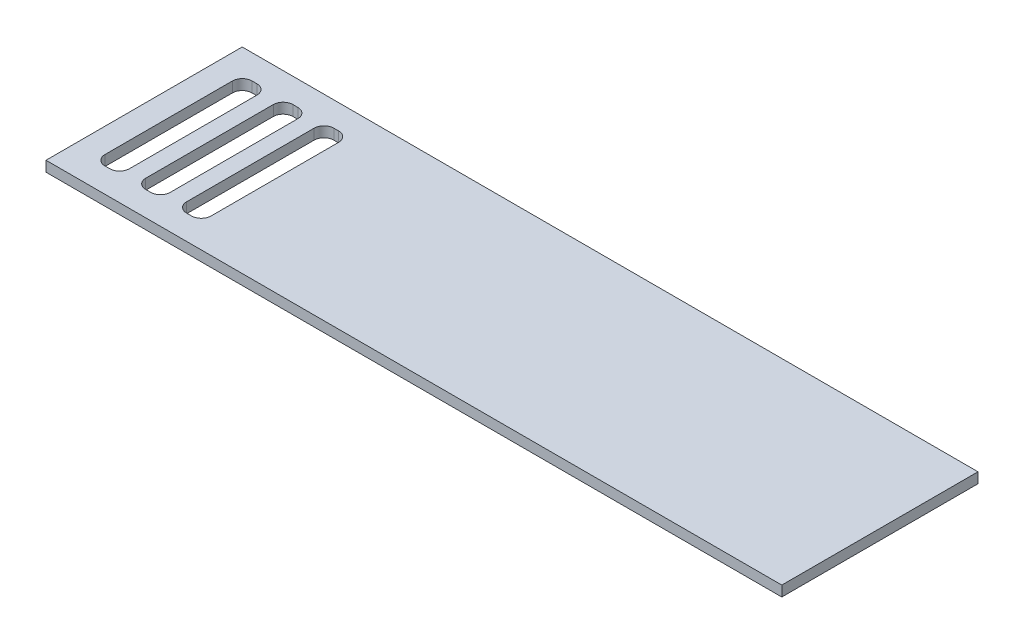
SolidWorks part; units mm, degrees
ref_plane "Front Plane" through (0, 0, 0) normal (0, 0, 1) x (1, 0, 0)
ref_plane "Top Plane" through (0, 0, 0) normal (0, 1, 0) x (1, 0, 0)
ref_plane "Right Plane" through (0, 0, 0) normal (1, 0, 0) x (0, 0, -1)
sketch "Sketch1" plane through (0, 0, 0) normal (0, 1, 0) x (1, 0, 0)
  line L1 (0, 0) -> (450, 0)
  line L2 (0, 0) -> (0, 120)
  line L3 (0, 120) -> (450, 120)
  line L4 (450, 0) -> (450, 120)
extrude "Boss-Extrude1" add sketch "Sketch1" along normal blind 6.35
sketch "Sketch2" plane through (0, 6.35, 0) normal (0, 1, 0) x (1, 0, 0)
  line L5 (15, 15) -> (15, 105)
  line L6 (15, 105) -> (30, 105)
  line L7 (30, 105) -> (30, 15)
  line L8 (30, 15) -> (15, 15)
  line L10 (40, 105) -> (55, 105)
  line L11 (55, 105) -> (55, 15)
  line L12 (55, 15) -> (40, 15)
  line L13 (40, 15) -> (40, 105)
  line L15 (65, 105) -> (65, 15)
  line L16 (65, 15) -> (80, 15)
  line L17 (80, 15) -> (80, 105)
  line L18 (80, 105) -> (65, 105)
extrude "Cut-Extrude1" cut sketch "Sketch2" against normal through all both and the other way through all
fillet "Fillet1" radius 6 12 edges at (80, 3.175, -15) (55, 3.175, -15) (30, 3.175, -15) (65, 3.175, -15) (40, 3.175, -15) (15, 3.175, -15) (15, 3.175, -105) (40, 3.175, -105) (65, 3.175, -105) (30, 3.175, -105) (55, 3.175, -105) (80, 3.175, -105)
